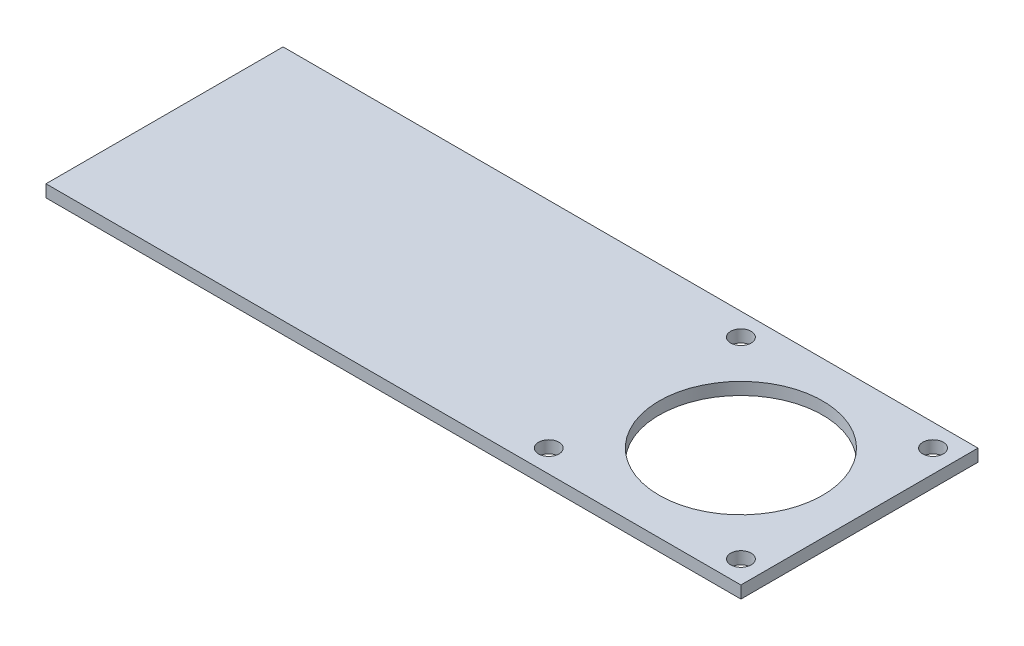
SolidWorks part; units mm, degrees
material "1060 Alloy"
ref_plane "Front Plane" through (0, 0, 0) normal (0, 0, 1) x (1, 0, 0)
ref_plane "Top Plane" through (0, 0, 0) normal (0, 1, 0) x (1, 0, 0)
ref_plane "Right Plane" through (0, 0, 0) normal (1, 0, 0) x (0, 0, -1)
sketch "Sketch1" plane through (0, 0, 0) normal (0, 0, 1) x (1, 0, 0)
  line L1 (-91.0636, 0) -> (78.9364, 0)
  line L2 (-91.0636, 0) -> (-91.0636, -3)
  line L3 (-91.0636, -3) -> (78.9364, -3)
  line L4 (78.9364, 0) -> (78.9364, -3)
  dimension "D1" = 3
  dimension "D2" = 170
extrude "Boss-Extrude1" add sketch "Sketch1" along normal blind 58
sketch "Sketch2" plane through (0, 0, 0) normal (0, 1, 0) x (1, 0, 0)
  line L0 (78.9364, 0) -> (73.4364, 0) construction
  line L1 (78.9364, 0) -> (-91.0636, 0) construction
  line L2 (73.4364, 0) -> (73.4364, -5.5) construction
  line L3 (78.9364, -29) -> (9.5823, -29) construction
  line L4 (78.9364, -58) -> (78.9364, 0) construction
  line L5 (78.9364, -58) -> (49.9364, -58) construction
  line L6 (78.9364, -58) -> (-91.0636, -58) construction
  line L7 (49.9364, -58) -> (49.9364, 0) construction
  circle A0 centre (73.4364, -5.5) radius 2.5
  circle A1 centre (73.4364, -52.5) radius 2.5
  circle A2 centre (26.4364, -52.5) radius 2.5
  circle A3 centre (26.4364, -5.5) radius 2.5
  circle A4 centre (49.9364, -29) radius 20
  dimension "D4" = 5
  dimension "D5" = 40
  dimension "D1" = 5.5
  dimension "D2" = 5.5
  dimension "D3" = 29
extrude "Cut-Extrude1" cut sketch "Sketch2" against normal blind 58
